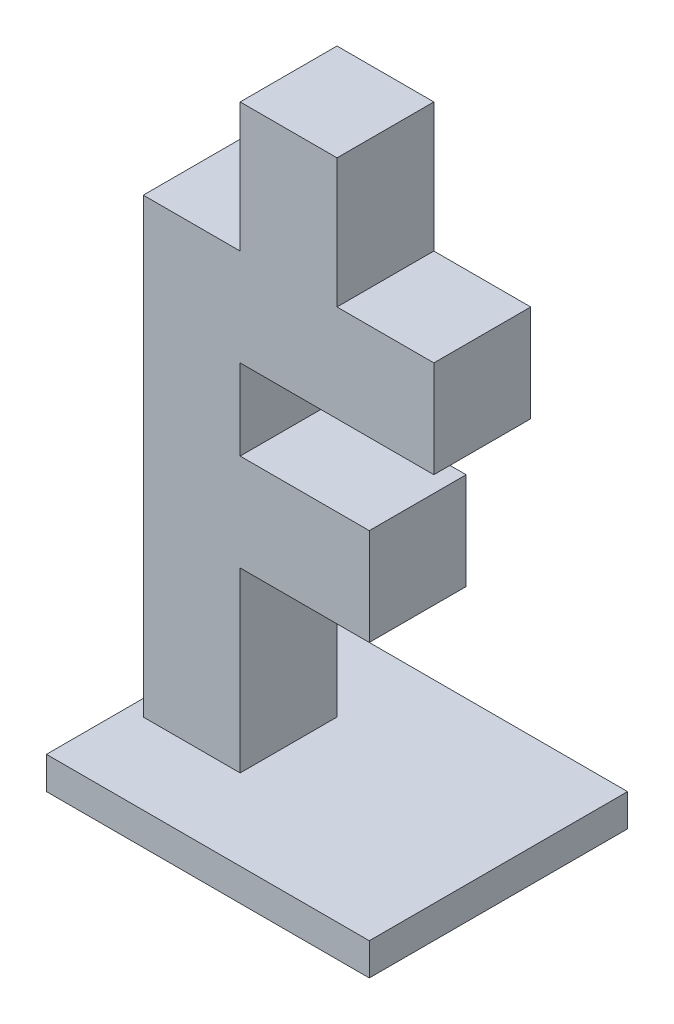
SolidWorks part; units mm, degrees
ref_plane "Vorne" through (0, 0, 0) normal (0, 0, 1) x (1, 0, 0)
ref_plane "Oben" through (0, 0, 0) normal (0, 1, 0) x (1, 0, 0)
ref_plane "Rechts" through (0, 0, 0) normal (1, 0, 0) x (0, 0, -1)
sketch "Skizze1" plane through (0, 0, 0) normal (0, 0, 1) x (1, 0, 0)
  line L0 (0, 0) -> (0, 70)
  line L1 (0, 70) -> (15, 70)
  line L2 (45, 70) -> (45, 55)
  line L3 (45, 55) -> (15, 55)
  line L4 (15, 55) -> (15, 42.5)
  line L5 (15, 42.5) -> (35, 42.5)
  line L6 (35, 42.5) -> (35, 27.5)
  line L7 (35, 27.5) -> (15, 27.5)
  line L8 (15, 27.5) -> (15, 0)
  line L9 (15, 0) -> (0, 0)
  line L10 (-41.8978, 35) -> (82.5182, 35) construction
  line L11 (22.5, 91.3402) -> (22.5, -17.9215) construction
  line L12 (30, 70) -> (45, 70)
  line L13 (15, 90) -> (30, 90)
  line L14 (15, 90) -> (15, 70)
  line L16 (30, 90) -> (30, 70)
  dimension "D1" = 70
  dimension "D2" = 15
  dimension "D3" = 15
  dimension "D4" = 15
  dimension "D5" = 45
  dimension "D6" = 20
  dimension "D7" = 20
  dimension "D8" = 15
extrude "Aufsatz-Linear austragen1" add sketch "Skizze1" along normal blind 15
sketch "Skizze2" plane through (0, 0, 0) normal (0, -1, 0) x (1, 0, 0)
  line L0 (-10.8619, 7.5) -> (52.3992, 7.5) construction
  line L1 (22.5, 25.0644) -> (22.5, -9.4589) construction
  line L2 (0, 15) -> (0, 0) construction
  line L3 (45, 15) -> (45, 0) construction
  line L4 (0, 0) -> (15, 0) construction
  line L5 (0, 15) -> (15, 15) construction
  line L7 (-2.5, 27.5) -> (47.5, 27.5)
  line L8 (-2.5, 27.5) -> (-2.5, -12.5)
  line L9 (-2.5, -12.5) -> (47.5, -12.5)
  line L10 (47.5, 27.5) -> (47.5, -12.5)
  dimension "D1" = 40
  dimension "D2" = 50
extrude "Aufsatz-Linear austragen2" add sketch "Skizze2" along normal blind 5
